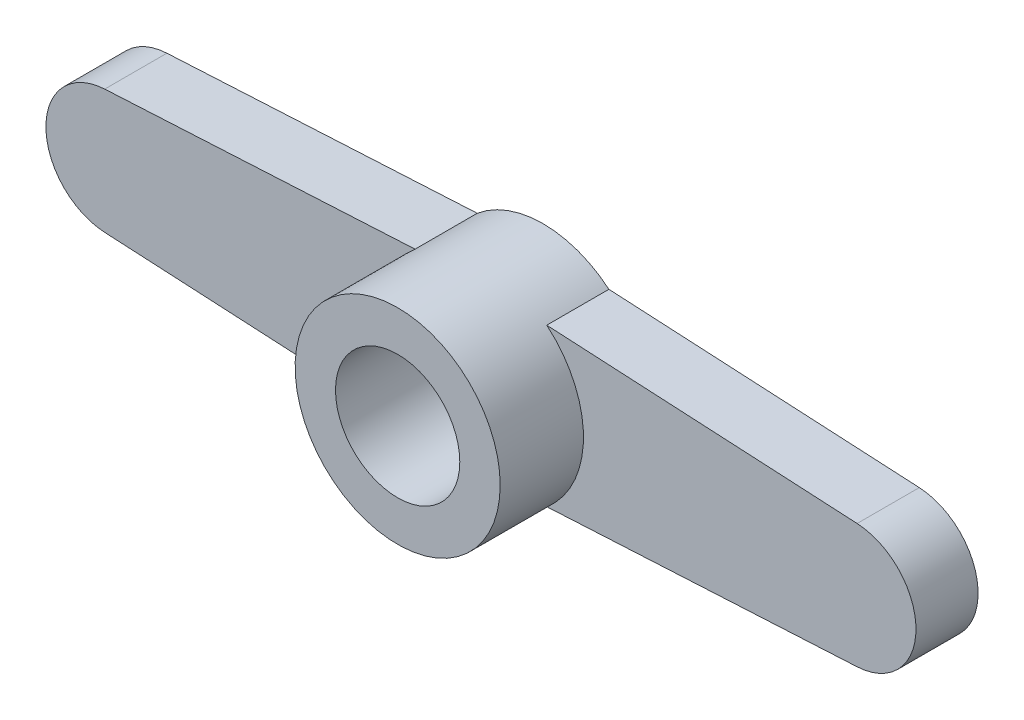
SolidWorks part; units mm, degrees
ref_plane "Спереди" through (0, 0, 0) normal (0, 0, 1) x (1, 0, 0)
ref_plane "Сверху" through (0, 0, 0) normal (0, 1, 0) x (1, 0, 0)
ref_plane "Справа" through (0, 0, 0) normal (1, 0, 0) x (0, 0, -1)
sketch "Эскиз1" plane through (0, 0, 0) normal (0, 0, 1) x (1, 0, 0)
  line L0 (0, 0) -> (-12, 0)
  line L1 (-2.1187, 2.53) -> (0, 2.643)
  line L2 (-2.1187, -2.53) -> (0, -2.643)
  line L3 (-12.1065, -1.9972) -> (-2.1187, -2.53)
  line L4 (0, 0) -> (0, 2) construction
  line L5 (12.1065, -1.9972) -> (2.1187, -2.53)
  line L6 (-12.1065, 1.9972) -> (-2.1187, 2.53)
  line L7 (12.1065, 1.9972) -> (2.1187, 2.53)
  circle A0 centre (0, 0) radius 3.3
  circle A1 centre (0, 0) radius 2
  arc A2 (-11.967, -1.9997) -> (-12.1065, 1.9972) centre (-12, 0) cw
  arc A3 (11.967, -1.9997) -> (12.1065, 1.9972) centre (12, 0) ccw
  dimension "D1" = 6.6
  dimension "D2" = 4
  dimension "D4" = 2
  dimension "D3" = 12
  dimension "D5" = 5.06
extrude "Бобышка-Вытянуть3" add sketch "Эскиз1" along normal blind 2
sketch "Croquis1" plane through (0, 0, 2) normal (0, 0, 1) x (1, 0, 0)
  circle A0 centre (0, 0) radius 3.3 construction
  circle A1 centre (0, 0) radius 3.3
  circle A2 centre (0, 0) radius 2 construction
  circle A3 centre (0, 0) radius 2
extrude "Saliente-Extruir1" add sketch "Croquis1" along normal offset from surface (2.68 mm away) 4.68 up to face at (0, 0, 0)
sketch "Эскиз5" plane through (0, 0, 0) normal (0, 0, -1) x (-1, 0, 0)
  circle A0 centre (0, 0) radius 2.5
extrude "Бобышка-Вытянуть7" add sketch "Эскиз5" against normal blind 1
sketch "Croquis2" plane through (0, 0, 1) normal (0, 0, 1) x (1, 0, 0)
  circle A0 centre (0, 0) radius 1.25
  dimension "D1" = 2.5
extrude "Cortar-Extruir1" cut sketch "Croquis2" against normal through all both and the other way through all
sketch "Croquis3" plane through (0, 0, 0) normal (0, 0, -1) x (-1, 0, 0)
  circle A0 centre (0, 0) radius 2.35
  dimension "D1" = 4.7
extrude "Cortar-Extruir2" cut sketch "Croquis3" against normal blind 1
